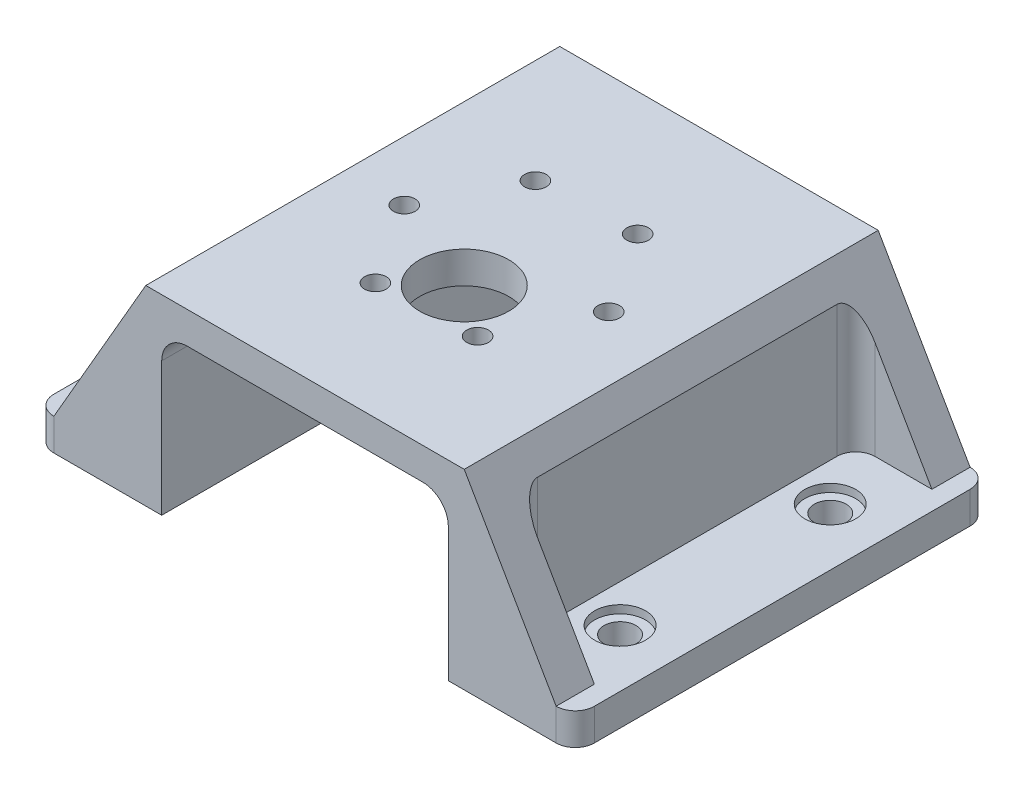
SolidWorks part; units mm, degrees
ref_plane "Front Plane" through (0, 0, 0) normal (0, 0, 1) x (1, 0, 0)
ref_plane "Top Plane" through (0, 0, 0) normal (0, 1, 0) x (1, 0, 0)
ref_plane "Right Plane" through (0, 0, 0) normal (1, 0, 0) x (0, 0, -1)
sketch "Sketch1" plane through (0, 0, 0) normal (0, 1, 0) x (1, 0, 0)
  line L1 (25, -25) -> (-25, -25)
  line L2 (25, -25) -> (25, 25)
  line L3 (25, 25) -> (-25, 25)
  line L4 (-25, -25) -> (-25, 25)
  line L5 (25, -25) -> (-25, 25) construction
  line L6 (25, 25) -> (-25, -25) construction
  point P0 (0, 0)
  dimension "D1" = 50
  dimension "D2" = 50
extrude "Boss-Extrude1" add sketch "Sketch1" along normal blind 30
sketch "Sketch2" plane through (0, 30, 0) normal (0, 1, 0) x (1, 0, 0)
  circle A0 centre (0, 0) radius 7
extrude "Cut-Extrude1" cut sketch "Sketch2" against normal blind 30
sketch "Sketch3" plane through (0, 0, 0) normal (0, -1, 0) x (1, 0, 0)
  circle A0 centre (6.6177, -20.6107) radius 1.7
  circle A1 centre (14.927, -7.7637) radius 1.7
  circle A2 centre (7.9559, 5.8559) radius 1.7
  circle A3 centre (-7.3246, 6.6285) radius 1.7
  circle A4 centre (-15.634, -6.2185) radius 1.7
  circle A5 centre (-8.6628, -19.8381) radius 1.7
extrude "Cut-Extrude2" cut sketch "Sketch3" against normal blind 42
sketch "Sketch5" plane through (0, 30, 0) normal (0, 1, 0) x (1, 0, 0)
  line L0 (25, -25) -> (25, 25) construction
  line L1 (-25, 25) -> (25, 25)
  line L2 (-25, 25) -> (-25, 40)
  line L3 (-25, 40) -> (25, 40)
  line L4 (25, 25) -> (25, 40)
  dimension "D1" = 0
  dimension "D2" = 15
extrude "Boss-Extrude2" add sketch "Sketch5" against normal blind 30
sketch "Sketch6" plane through (0, 0, 25) normal (0, 0, 1) x (1, 0, 0)
  line L0 (-25, 30) -> (-42.3205, 0)
  line L1 (-42.3205, 0) -> (-25, 0)
  line L2 (-25, 30) -> (-25, 0)
  dimension "D1" = 60
extrude "Boss-Extrude3" add sketch "Sketch6" against normal blind 65
mirror "Mirror1" about plane through (0, 0, 0) normal (1, 0, 0) of "Boss-Extrude3"
sketch "Sketch7" plane through (0, 0, 25) normal (0, 0, 1) x (1, 0, 0)
  line L1 (22.5, -17.253) -> (-22.5, -17.253)
  line L2 (22.5, -17.253) -> (22.5, 25)
  line L3 (22.5, 25) -> (-22.5, 25)
  line L4 (-22.5, -17.253) -> (-22.5, 25)
  line L5 (22.5, -17.253) -> (-22.5, 25) construction
  line L6 (22.5, 25) -> (-22.5, -17.253) construction
  line L7 (-25, 30) -> (25, 30) construction
  point P6 (0, 3.8735)
  dimension "D1" = 5
  dimension "D2" = 45
  dimension "D3" = 0
extrude "Cut-Extrude3" cut sketch "Sketch7" against normal blind 66
fillet "Fillet1" radius 4 2 edges at (-22.5, 25, -7.5) (22.5, 25, -7.5)
ref_plane "Plane1" through (0, 0, 19) normal (0, 0, 1) x (1, 0, 0)
sketch "Sketch9" plane through (0, 0, 19) normal (0, 0, 1) x (1, 0, 0)
  line L0 (39.4338, 5) -> (27.5, 5)
  line L1 (25, 30) -> (42.3205, 0) construction
  line L2 (27.5, 5) -> (27.5, 25.6699)
  line L3 (27.5, 25.6699) -> (39.4338, 5)
  line L4 (22.5, 0) -> (42.3205, 0) construction
  line L5 (22.5, 0) -> (22.5, 21) construction
  line L6 (27.5, 25.6699) -> (39.4338, 5)
  point P7 (32.4103, 0)
  dimension "D1" = 5
  dimension "D2" = 5
extrude "Cut-Extrude4" cut sketch "Sketch9" against normal blind 53 contours L3 L2 L0
mirror "Mirror2" about plane through (0, 0, 0) normal (1, 0, 0) of "Cut-Extrude4"
sketch "Sketch10" plane through (0, 5, 0) normal (0, 1, 0) x (1, 0, 0)
  line L0 (39.4338, 34) -> (27.5, 34) construction
  line L1 (-16.5, -19) -> (16.5, -19) construction
  line L2 (0, -16.5) -> (0, 16.5) construction
  circle A0 centre (33.4669, 24) radius 4
  circle A1 centre (33.4669, -9) radius 4
  circle A2 centre (-33.4669, -9) radius 4
  circle A3 centre (-33.4669, 24) radius 4
  dimension "D1" = 10
  dimension "D2" = 10
extrude "Cut-Extrude5" cut sketch "Sketch10" against normal blind 1.25
sketch "Sketch11" plane through (0, 3.75, 0) normal (0, 1, 0) x (1, 0, 0)
  line L0 (0, -16.5) -> (0, 16.5) construction
  circle A0 centre (33.4669, 24) radius 2.5
  circle A1 centre (33.4669, -9) radius 2.5
  circle A2 centre (-33.4669, -9) radius 2.5
  circle A3 centre (-33.4669, 24) radius 2.5
extrude "Cut-Extrude6" cut sketch "Sketch11" against normal blind 36.25
sketch "Sketch12" plane through (0, 0, 25) normal (0, 0, 1) x (1, 0, 0)
  line L0 (42.3205, 0) -> (39.4338, 5)
  line L1 (39.4338, 5) -> (39.4338, 0)
  line L2 (22.5, 0) -> (42.3205, 0) construction
  line L3 (39.4338, 0) -> (42.3205, 0)
extrude "Cut-Extrude7" cut sketch "Sketch12" against normal blind 90.25
mirror "Mirror3" about plane through (0, 0, 0) normal (1, 0, 0) of "Cut-Extrude7"
fillet "Fillet2" radius 3 4 edges at (27.5, 15.3349, -34) (27.5, 15.3349, 19) (-27.5, 15.3349, 19) (-27.5, 15.3349, -34)
sketch "Sketch13" plane through (0, 0, 25) normal (0, 0, 1) x (1, 0, 0)
  line L1 (39.4338, 0) -> (42.4338, 0)
  line L2 (39.4338, 0) -> (39.4338, 5)
  line L3 (39.4338, 5) -> (42.4338, 5)
  line L4 (42.4338, 0) -> (42.4338, 5)
  dimension "D1" = 3
extrude "Boss-Extrude4" add sketch "Sketch13" against normal blind 65
mirror "Mirror4" about plane through (0, 0, 0) normal (1, 0, 0) of "Boss-Extrude4"
fillet "Fillet3" radius 3 8 edges at (40.9338, 5, -40) (42.4338, 2.5, -40) (42.4338, 2.5, 25) (40.9338, 5, 25) (-42.4338, 2.5, 25) (-40.9338, 5, 25) (-42.4338, 2.5, -40) (-40.9338, 5, -40)
